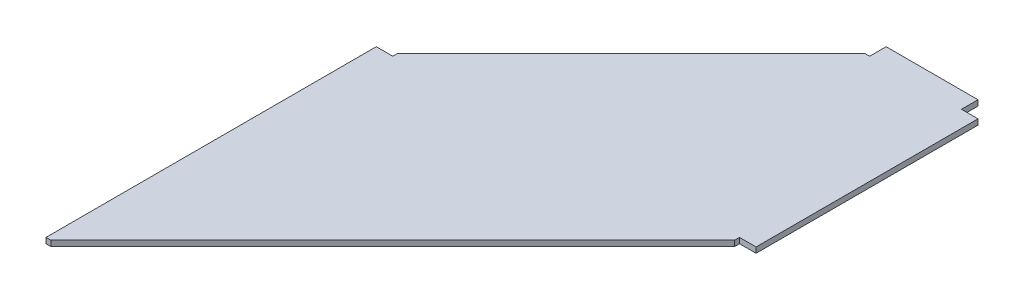
SolidWorks part; units mm, degrees
material "Pine"
ref_plane "Front Plane" through (0, 0, 0) normal (0, 0, 1) x (1, 0, 0)
ref_plane "Top Plane" through (0, 0, 0) normal (0, 1, 0) x (1, 0, 0)
ref_plane "Right Plane" through (0, 0, 0) normal (1, 0, 0) x (0, 0, -1)
sketch "Sketch1" plane through (0, 0, 0) normal (0, 1, 0) x (1, 0, 0)
  line L0 (97.7477, 198.9481) -> (135.8477, 198.9481) construction
  line L1 (-452.2523, 237.0481) -> (385.8477, 237.0481) construction
  line L2 (-452.2523, 237.0481) -> (-452.2523, -351.0519) construction
  line L3 (-452.2523, -1112.9519) -> (385.8477, -1112.9519) construction
  line L4 (385.8477, 237.0481) -> (385.8477, -1112.9519) construction
  line L5 (385.8477, 237.0481) -> (347.7477, 237.0481) construction
  line L6 (385.8477, 237.0481) -> (385.8477, 198.9481) construction
  line L7 (385.8477, 198.9481) -> (347.7477, 198.9481) construction
  line L8 (347.7477, 237.0481) -> (347.7477, 198.9481) construction
  line L9 (135.8477, 237.0481) -> (97.7477, 237.0481) construction
  line L10 (135.8477, 237.0481) -> (135.8477, 198.9481) construction
  line L12 (97.7477, 237.0481) -> (97.7477, 198.9481) construction
  line L13 (124.6477, 198.9481) -> (-414.1523, -339.8519)
  line L14 (135.8477, 198.9481) -> (135.8477, 237.0481)
  line L15 (135.8477, 237.0481) -> (347.7477, 237.0481)
  line L16 (347.7477, 237.0481) -> (347.7477, 198.9481)
  line L17 (347.7477, 198.9481) -> (385.8477, 198.9481)
  line L18 (-452.2523, -1112.9519) -> (-441.0523, -1112.9519)
  line L19 (347.7477, -324.2519) -> (-441.0523, -1112.9519)
  line L20 (385.8477, -313.0519) -> (385.8477, 198.9481)
  line L21 (-452.2523, -1112.9519) -> (-452.2523, -351.0519)
  line L22 (385.8477, -313.0519) -> (347.7477, -313.0519) construction
  line L23 (385.8477, -313.0519) -> (385.8477, -351.1519) construction
  line L24 (385.8477, -351.1519) -> (347.7477, -351.1519) construction
  line L25 (347.7477, -313.0519) -> (347.7477, -351.1519) construction
  line L26 (347.7477, -324.2519) -> (347.7477, -313.0519)
  line L27 (347.7477, -313.0519) -> (385.8477, -313.0519)
  line L28 (-452.2523, -351.0519) -> (-414.1523, -351.0519)
  line L29 (-452.2523, -351.0519) -> (-414.1523, -351.0519) construction
  line L30 (-452.2523, -351.0519) -> (-452.2523, -312.9519) construction
  line L31 (-452.2523, -312.9519) -> (-414.1523, -312.9519) construction
  line L32 (-414.1523, -351.0519) -> (-414.1523, -312.9519) construction
  line L33 (-414.1523, -351.0519) -> (-414.1523, -339.8519)
  line L34 (124.6477, 198.9481) -> (135.8477, 198.9481)
  point P7 (135.8477, 237.0481)
  point P12 (124.6477, 198.9481)
  point P15 (-441.0523, -1112.9519)
  point P21 (347.7477, -324.2519)
  point P23 (-452.2523, -351.0519)
  point P28 (-414.1523, -339.8519)
  point P29 (-414.1523, -339.8519)
  dimension "D1" = 838.1
  dimension "D2" = 1350
  dimension "D3" = 38.1
  dimension "D4" = 38.1
  dimension "D5" = 211.9
  dimension "D6" = 38.1
  dimension "D7" = 38.1
  dimension "D8" = 11.2
  dimension "D9" = 11.2
  dimension "D10" = 512
  dimension "D11" = 38.1
  dimension "D12" = 38.1
  dimension "D13" = 11.2
  dimension "D14" = 761.9
  dimension "D15" = 38.1
  dimension "D16" = 38.1
  dimension "D17" = 11.2
extrude "Boss-Extrude1" add sketch "Sketch1" along normal blind 12.7
